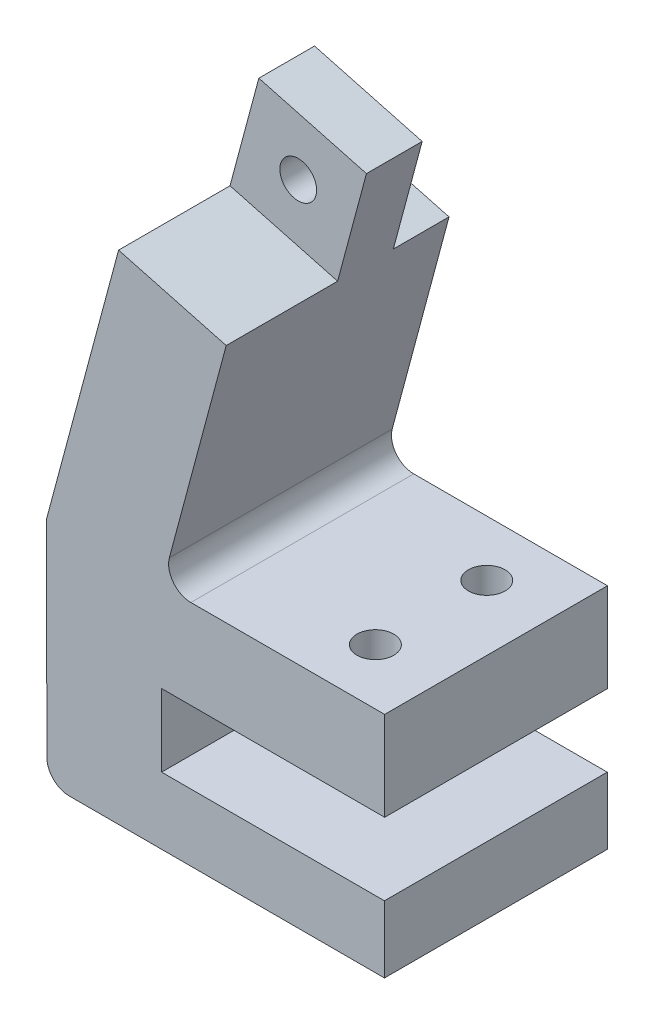
SolidWorks part; units mm, degrees
ref_plane "前视基准面" through (0, 0, 0) normal (0, 0, 1) x (1, 0, 0)
ref_plane "上视基准面" through (0, 0, 0) normal (0, 1, 0) x (1, 0, 0)
ref_plane "右视基准面" through (0, 0, 0) normal (1, 0, 0) x (0, 0, -1)
other "Configuration Table"
sketch "草图1" plane through (0, 0, 0) normal (0, 0, 1) x (1, 0, 0)
  line L0 (0.0201, -0.0524) -> (0.0169, 5.9476)
  line L1 (0.0169, 5.9476) -> (-19.9831, 5.9476)
  line L2 (-19.9831, 5.9476) -> (-20.0001, 12.4476)
  line L3 (-20.0001, 12.4476) -> (0.0376, 12.4476)
  line L4 (0.0376, 12.4476) -> (0.0376, 20.4476)
  line L5 (0.0376, 20.4476) -> (-19.9624, 20.4476)
  line L6 (-19.9624, 20.4476) -> (-11.5972, 51.6668)
  line L8 (-21.2565, 54.255) -> (-30.3152, 20.4476)
  line L9 (-30.3152, 20.4476) -> (-30.2797, -0.0524)
  line L10 (-30.2797, -0.0524) -> (0.0201, -0.0524)
  line L11 (-21.2565, 54.255) -> (-11.5972, 51.6668)
  line L19 (-19.9624, 20.4476) -> (-29.6217, 23.0358) construction
  dimension "D1" = 8
  dimension "D2" = 6
  dimension "D3" = 6.5
  dimension "D4" = 75
  dimension "D5" = 35
  dimension "D6" = 20
  dimension "D7" = 20
  dimension "D11" = 32.3205
extrude "凸台-拉伸1" add sketch "草图1" along normal blind 20
fillet "圆角1" radius 2 1 edges at (-19.9624, 20.4476, 10)
fillet "圆角2" radius 2 1 edges at (-30.2797, -0.0524, 10)
sketch "草图20" plane through (0, 0, 20) normal (0, 0, 1) x (1, 0, 0)
  line L0 (-11.5972, 51.6668) -> (-11.5972, 12.4476) construction
  line L1 (-20.0001, 12.4476) -> (0.0376, 12.4476) construction
sketch "草图22" plane through (0, 12.4476, 0) normal (0, -1, 0) x (1, 0, 0)
  line L1 (-11.5972, 20) -> (0, 20) construction
  line L2 (-11.5972, 20) -> (-11.5972, 0) construction
  line L3 (-11.5972, 0) -> (0, 0) construction
  line L4 (0, 20) -> (0, 0) construction
  line L5 (-11.5972, 20) -> (0, 20) construction
  line L6 (-11.5972, 20) -> (-11.5972, 10) construction
  line L7 (-11.5972, 10) -> (0, 10) construction
  line L8 (0, 20) -> (0, 10) construction
  line L9 (-11.5972, 20) -> (0, 10) construction
  line L10 (-11.5972, 10) -> (0, 20) construction
  line L11 (-11.5972, 10) -> (0, 10) construction
  line L12 (-11.5972, 10) -> (-11.5972, 0) construction
  line L13 (-11.5972, 0) -> (0, 0) construction
  line L14 (0, 10) -> (0, 0) construction
  line L15 (-11.5972, 10) -> (0, 0) construction
  line L16 (-11.5972, 0) -> (0, 10) construction
  point P4 (-5.7986, 10)
  point P9 (-5.7986, 15)
  point P11 (-5.7986, 5)
sketch "草图33" plane through (0, 0, 20) normal (0, 0, 1) x (1, 0, 0)
  line L0 (-21.2565, 54.255) -> (-11.5972, 51.6668)
  line L1 (-21.2565, 54.255) -> (-23.8447, 44.5958)
  line L2 (-11.5972, 51.6668) -> (-14.1854, 42.0076)
  line L3 (-23.8447, 44.5958) -> (-14.1854, 42.0076)
  line L4 (-21.2565, 54.255) -> (-14.1854, 42.0076) construction
  line L5 (-11.5972, 51.6668) -> (-23.8447, 44.5958) construction
  point P6 (-17.721, 48.1313)
  dimension "D1" = 10
extrude "切除-拉伸2" cut sketch "草图33" against normal blind 10
sketch "草图34" plane through (0, 0, 0) normal (0, 0, -1) x (-1, 0, 0)
  line L0 (11.5972, 51.6668) -> (21.2565, 54.255) construction
  line L1 (11.5972, 51.6668) -> (14.1854, 42.0076) construction
  line L2 (21.2565, 54.255) -> (23.8447, 44.5958) construction
  line L3 (14.1854, 42.0076) -> (23.8447, 44.5958) construction
  line L4 (11.5972, 51.6668) -> (23.8447, 44.5958) construction
  line L5 (21.2565, 54.255) -> (14.1854, 42.0076) construction
  circle A0 centre (17.721, 48.1313) radius 3.25
  point P6 (17.721, 48.1313)
  dimension "D2" = 6.5
  dimension "D1" = 10
extrude "切除-拉伸3" cut sketch "草图34" against normal blind 6
hole_wizard "M4 螺纹孔的螺纹孔钻头2" positions "草图37" profile "草图36" hole size "M4" standard "ISO" end condition up to next
sketch "草图37" plane through (0, 0, 6) normal (0, 0, -1) x (-1, 0, 0)
  point P0 (17.721, 48.1313)
sketch "草图36" plane through (-17.721, 48.1313, 6) normal (1, 0, 0) x (0, 1, 0)
  line L0 (0, 0) -> (0, 4)
  line L1 (0, 4) -> (1.65, 4)
  line L2 (1.65, 4) -> (1.65, 0)
  line L5 (1.65, 0) -> (0, 0)
  line L11 (0, -6.35) -> (0, 107.95) construction
  dimension "通孔孔直径" = 3.3
  dimension "通孔孔深度" = 4
sketch "草图38" plane through (-23.7371, 6.3603, 0) normal (0.9659, -0.2588, 0) x (0, 0, -1)
  line L1 (0, 46.9048) -> (-5, 46.9048)
  line L2 (0, 46.9048) -> (0, 36.9048)
  line L3 (0, 36.9048) -> (-5, 36.9048)
  line L4 (-5, 46.9048) -> (-5, 36.9048)
  line L5 (0, 46.9048) -> (-5, 36.9048) construction
  line L6 (0, 36.9048) -> (-5, 46.9048) construction
  point P4 (-2.5, 41.9048)
  dimension "D1" = 5
extrude "切除-拉伸4" cut sketch "草图38" against normal blind 11
hole_wizard "M4 螺纹孔的螺纹孔钻头3" positions "草图39" profile "草图40" hole size "M4" standard "ISO"
sketch "草图39" plane through (0, 12.4476, 0) normal (0, -1, 0) x (-1, 0, 0)
  point P0 (5.7986, -5)
  point P3 (5.7986, -15)
sketch "草图40" plane through (-5.7986, 12.4476, 5) normal (1, 0, 0) x (0, 0, -1)
  line L0 (0, 0) -> (0, 8)
  line L1 (0, 8) -> (1.65, 8)
  line L2 (1.65, 8) -> (1.65, 0)
  line L5 (1.65, 0) -> (0, 0)
  line L11 (0, -6.35) -> (0, 107.95) construction
  dimension "通孔孔直径" = 3.3
  dimension "通孔孔深度" = 8
sketch "草图41" plane through (0, 12.4476, 0) normal (0, -1, 0) x (1, 0, 0)
  line L0 (-11.5972, 20) -> (0, 10) construction
  line L2 (-7.2658, 12.1) -> (-4.3315, 12.1)
  line L4 (-7.2658, 17.9) -> (-4.3315, 17.9)
  line L6 (-7.2658, 12.1) -> (-4.3315, 17.9) construction
  line L7 (-7.2658, 17.9) -> (-4.3315, 12.1) construction
  line L8 (-7.2658, 2.1) -> (-4.3315, 2.1)
  line L10 (-7.2658, 7.9) -> (-4.3315, 7.9)
  line L12 (-7.2658, 2.1) -> (-4.3315, 7.9) construction
  line L13 (-7.2658, 7.9) -> (-4.3315, 2.1) construction
  arc A0 (-7.2658, 17.9) -> (-7.2658, 12.1) centre (-5.7986, 15) ccw
  arc A1 (-7.2658, 7.9) -> (-7.2658, 2.1) centre (-5.7986, 5) ccw
  arc A2 (-4.3315, 12.1) -> (-4.3315, 17.9) centre (-5.7986, 15) ccw
  arc A3 (-4.3315, 2.1) -> (-4.3315, 7.9) centre (-5.7986, 5) ccw
  dimension "D1" = 6.5
  dimension "D2" = 6.5
  dimension "D3" = 5.8
  dimension "D4" = 5.8
extrude "切除-拉伸5" cut sketch "草图41" against normal blind 4.5
